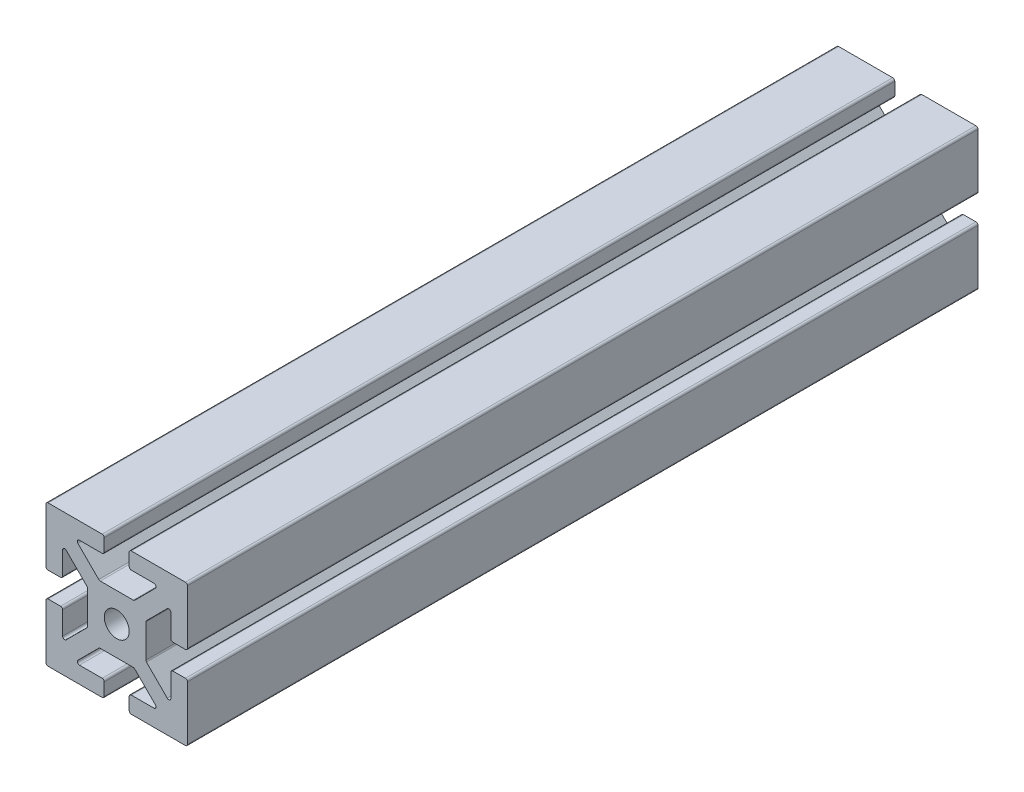
SolidWorks part; units mm, degrees
material "6061-T4 (SS)"
ref_plane "Front Plane" through (0, 0, 0) normal (0, 0, 1) x (1, 0, 0)
ref_plane "Top Plane" through (0, 0, 0) normal (0, 1, 0) x (1, 0, 0)
ref_plane "Right Plane" through (0, 0, 0) normal (1, 0, 0) x (0, 0, -1)
sketch "Sketch1" plane through (0, 0, 0) normal (0, 0, 1) x (1, 0, 0)
  line L0 (1.5, -8.25) -> (1.5, -6.75)
  line L1 (1.9822, -3.5) -> (-1.9822, -3.5)
  line L2 (3.5, -1.9822) -> (3.5, 1.9822)
  line L3 (1.9822, 3.5) -> (-1.9822, 3.5)
  line L4 (-3.5, -1.9822) -> (-3.5, 1.9822)
  line L7 (6.5, -6.5) -> (-6.5, -6.5) construction
  line L8 (6.5, -6.5) -> (6.5, 6.5) construction
  line L9 (6.5, 6.5) -> (-6.5, 6.5) construction
  line L10 (-6.5, -6.5) -> (-6.5, 6.5) construction
  line L11 (6.5, -6.5) -> (-6.5, 6.5) construction
  line L12 (6.5, 6.5) -> (-6.5, -6.5) construction
  line L13 (8.5, -8.5) -> (-8.5, -8.5) construction
  line L14 (8.5, -8.5) -> (8.5, 8.5) construction
  line L15 (8.5, 8.5) -> (-8.5, 8.5) construction
  line L16 (-8.5, -8.5) -> (-8.5, 8.5) construction
  line L17 (8.5, -8.5) -> (-8.5, 8.5) construction
  line L18 (8.5, 8.5) -> (-8.5, -8.5) construction
  line L19 (-1.5, 8.5) -> (1.5, 8.5) construction
  line L20 (1.75, 8.5) -> (8.25, 8.5)
  line L21 (0, 0) -> (0, 50000) construction
  line L22 (1.75, -6.5) -> (4.4822, -6.5)
  line L23 (8.5, 8.25) -> (8.5, 1.75)
  line L24 (1.5, 8.25) -> (1.5, 6.75)
  line L25 (1.75, 6.5) -> (4.4822, 6.5)
  line L26 (4.659, 6.0732) -> (2.159, 3.5732)
  line L27 (8.25, 1.5) -> (6.75, 1.5)
  line L28 (6.5, 1.75) -> (6.5, 4.4822)
  line L29 (6.0732, 4.659) -> (3.5732, 2.159)
  line L30 (8.25, -8.5) -> (1.75, -8.5)
  line L31 (8.5, -1.75) -> (8.5, -8.25)
  line L32 (8.25, -1.5) -> (6.75, -1.5)
  line L33 (6.5, -1.75) -> (6.5, -4.4822)
  line L34 (6.0732, -4.659) -> (3.5732, -2.159)
  line L35 (4.659, -6.0732) -> (2.159, -3.5732)
  line L36 (-8.25, -1.5) -> (-6.75, -1.5)
  line L37 (-6.5, -1.75) -> (-6.5, -4.4822)
  line L38 (-8.5, -8.25) -> (-8.5, -1.75)
  line L39 (-1.75, -8.5) -> (-8.25, -8.5)
  line L40 (-1.5, -8.25) -> (-1.5, -6.75)
  line L41 (-1.75, -6.5) -> (-4.4822, -6.5)
  line L42 (-4.659, -6.0732) -> (-2.159, -3.5732)
  line L43 (-6.0732, -4.659) -> (-3.5732, -2.159)
  line L44 (-1.5, 8.25) -> (-1.5, 6.75)
  line L45 (-1.75, 6.5) -> (-4.4822, 6.5)
  line L46 (-8.25, 8.5) -> (-1.75, 8.5)
  line L47 (-8.5, 1.75) -> (-8.5, 8.25)
  line L48 (-8.25, 1.5) -> (-6.75, 1.5)
  line L49 (-6.5, 1.75) -> (-6.5, 4.4822)
  line L50 (-6.0732, 4.659) -> (-3.5732, 2.159)
  line L51 (-4.659, 6.0732) -> (-2.159, 3.5732)
  circle A0 centre (0, 0) radius 1.5
  arc A1 (4.4822, 6.5) -> (4.659, 6.0732) centre (4.4822, 6.25) cw
  arc A2 (6.5, 4.4822) -> (6.0732, 4.659) centre (6.25, 4.4822) ccw
  arc A3 (6.75, 1.5) -> (6.5, 1.75) centre (6.75, 1.75) cw
  arc A4 (8.5, 1.75) -> (8.25, 1.5) centre (8.25, 1.75) cw
  arc A5 (8.25, 8.5) -> (8.5, 8.25) centre (8.25, 8.25) cw
  arc A6 (1.5, 6.75) -> (1.75, 6.5) centre (1.75, 6.75) ccw
  arc A7 (1.5, 8.25) -> (1.75, 8.5) centre (1.75, 8.25) cw
  arc A8 (1.5, -6.75) -> (1.75, -6.5) centre (1.75, -6.75) cw
  arc A9 (1.75, -8.5) -> (1.5, -8.25) centre (1.75, -8.25) cw
  arc A10 (8.5, -8.25) -> (8.25, -8.5) centre (8.25, -8.25) cw
  arc A11 (8.25, -1.5) -> (8.5, -1.75) centre (8.25, -1.75) cw
  arc A12 (6.75, -1.5) -> (6.5, -1.75) centre (6.75, -1.75) ccw
  arc A13 (6.5, -4.4822) -> (6.0732, -4.659) centre (6.25, -4.4822) cw
  arc A14 (4.4822, -6.5) -> (4.659, -6.0732) centre (4.4822, -6.25) ccw
  arc A15 (-6.75, -1.5) -> (-6.5, -1.75) centre (-6.75, -1.75) cw
  arc A16 (-8.5, -1.75) -> (-8.25, -1.5) centre (-8.25, -1.75) cw
  arc A17 (-8.25, -8.5) -> (-8.5, -8.25) centre (-8.25, -8.25) cw
  arc A18 (-1.5, -8.25) -> (-1.75, -8.5) centre (-1.75, -8.25) cw
  arc A19 (-1.5, -6.75) -> (-1.75, -6.5) centre (-1.75, -6.75) ccw
  arc A20 (-4.4822, -6.5) -> (-4.659, -6.0732) centre (-4.4822, -6.25) cw
  arc A21 (-6.5, -4.4822) -> (-6.0732, -4.659) centre (-6.25, -4.4822) ccw
  arc A22 (-1.5, 6.75) -> (-1.75, 6.5) centre (-1.75, 6.75) cw
  arc A23 (-1.75, 8.5) -> (-1.5, 8.25) centre (-1.75, 8.25) cw
  arc A24 (-8.5, 8.25) -> (-8.25, 8.5) centre (-8.25, 8.25) cw
  arc A25 (-8.25, 1.5) -> (-8.5, 1.75) centre (-8.25, 1.75) cw
  arc A26 (-6.75, 1.5) -> (-6.5, 1.75) centre (-6.75, 1.75) ccw
  arc A27 (-6.5, 4.4822) -> (-6.0732, 4.659) centre (-6.25, 4.4822) cw
  arc A28 (-4.4822, 6.5) -> (-4.659, 6.0732) centre (-4.4822, 6.25) ccw
  arc A29 (-2.159, 3.5732) -> (-1.9822, 3.5) centre (-1.9822, 3.75) ccw
  arc A30 (2.159, 3.5732) -> (1.9822, 3.5) centre (1.9822, 3.75) cw
  arc A31 (3.5732, 2.159) -> (3.5, 1.9822) centre (3.75, 1.9822) ccw
  arc A32 (3.5732, -2.159) -> (3.5, -1.9822) centre (3.75, -1.9822) cw
  arc A33 (2.159, -3.5732) -> (1.9822, -3.5) centre (1.9822, -3.75) ccw
  arc A34 (-2.159, -3.5732) -> (-1.9822, -3.5) centre (-1.9822, -3.75) cw
  arc A35 (-3.5732, -2.159) -> (-3.5, -1.9822) centre (-3.75, -1.9822) ccw
  arc A36 (-3.5732, 2.159) -> (-3.5, 1.9822) centre (-3.75, 1.9822) cw
  point P28 (5.0858, 6.5)
  point P31 (6.5, 5.0858)
  point P34 (6.5, 1.5)
  point P37 (8.5, 1.5)
  point P43 (1.5, 6.5)
  point P47 (-5.3399, 6)
  point P119 (0, 0)
  point P130 (0, 0)
  dimension "D1" = 3
  dimension "D7" = 0.25
  dimension "D9" = 0.25
  dimension "D2" = 3.5
  dimension "D3" = 3
  dimension "D4" = 2
  dimension "D5" = 3
  dimension "D6" = 2
  dimension "D8" = 4
extrude "Boss-Extrude1" add sketch "Sketch1" along normal blind 95 contours L50 A36 L4 A35 L43 A21 L37 A15 L36 A16 L38 A17 L39 A18 L40 A19 L41 A20 L42 A34 L1 A33 L35 A14 L22 A8 L0 A9 L30 A10 L31 A11 L32 A12 L33 A13 L34 A32 L2 A31 L29 A2 L28 A3 L27 A4 L23 A5 L20 A7 L24
equation "\"A\" = 2"
equation "\"B\" = 3"
equation "\"C\"= 95"
equation "\"D1@Sketch1\"=\"B\""
equation "\"FuckYou\"= ( \"B\" / 2 ) + \"A\""
equation "\"D2@Sketch1\"=\"FuckYou\""
equation "\"D3@Sketch1\"=\"B\""
equation "\"D5@Sketch1\"=\"B\""
equation "\"D1@Boss-Extrude1\"=\"C\""
equation "\"D4@Sketch1\"=\"A\""
equation "\"D6@Sketch1\"=\"A\""
